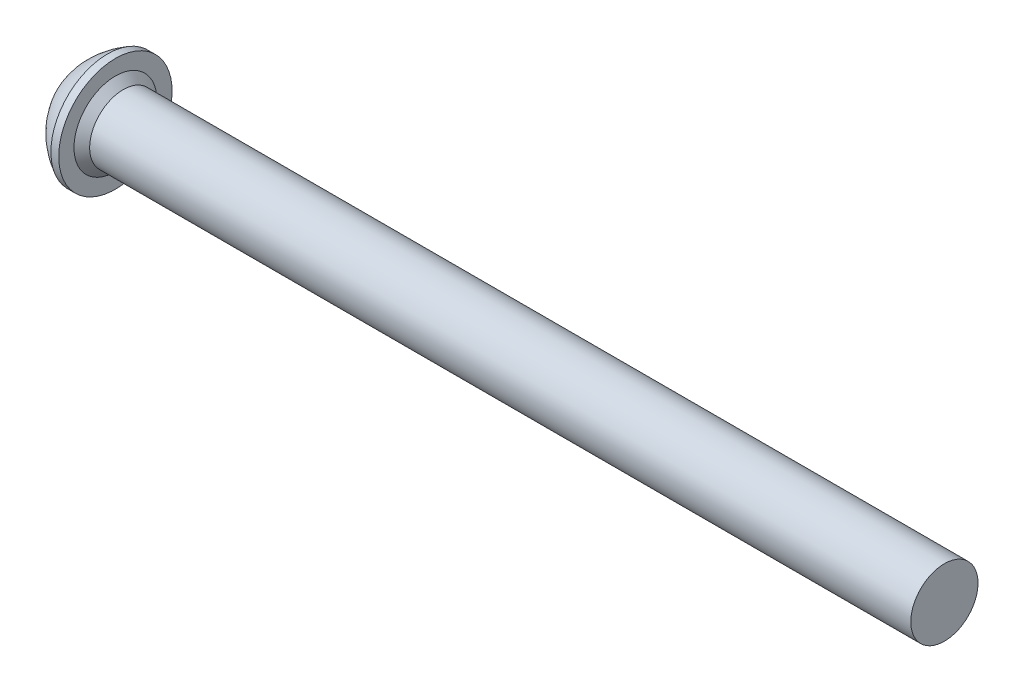
SolidWorks part; units mm, degrees
ref_plane "Front Plane" through (0, 0, 0) normal (0, 0, 1) x (1, 0, 0)
ref_plane "Top Plane" through (0, 0, 0) normal (0, 1, 0) x (1, 0, 0)
ref_plane "Right Plane" through (0, 0, 0) normal (1, 0, 0) x (0, 0, -1)
sketch "Sketch2" plane through (0, 0, 0) normal (0, 0, 1) x (1, 0, 0)
  line L0 (0, 0) -> (0, 1.43)
  line L2 (1.25, 2.53) -> (1.6, 2.53)
  line L3 (1.6, 2.53) -> (1.6, 1.85)
  line L4 (1.6, 1.85) -> (1.95, 1.5)
  line L5 (1.95, 1.5) -> (38.6, 1.5)
  line L6 (38.6, 1.5) -> (38.6, 0)
  line L7 (38.6, 0) -> (0, 0)
  arc A0 (1.25, 2.53) -> (0, 1.43) centre (2.8708, -0.5721) ccw
  point P10 (0.9983, 2.2125)
  point P11 (1.8687, 0.8411)
  point P12 (1.7013, 2.53)
  point P13 (1.95, 0.8645)
  point P14 (1.95, 0.835)
  point P15 (1.7135, 1.0417)
  point P16 (0.9606, 2.53)
  point P17 (1.6033, 1.8467)
  dimension "D4" = 3.5
  dimension "D1" = 1.43
  dimension "D2" = 1.95
  dimension "D3" = 0.35
  dimension "D5" = 2.53
  dimension "D6" = 135
  dimension "D7" = 1.5
  dimension "D8" = 0.35
  dimension "D9" = 37
revolve "Revolve1" add sketch "Sketch2" angle 360 about L7
sketch "Sketch3" plane through (0, 0, 0) normal (-1, 0, 0) x (0, 0, 1)
  line L0 (0, 2.3249) -> (0, -2.2676) construction
  line L2 (0, 1.1547) -> (-1, 0.5774)
  line L3 (-1, 0.5774) -> (-1, -0.5774)
  line L4 (-1, -0.5774) -> (0, -1.1547)
  line L5 (0, -1.1547) -> (1, -0.5774)
  line L6 (1, -0.5774) -> (1, 0.5774)
  line L7 (1, 0.5774) -> (0, 1.1547)
  circle A0 centre (0, 0) radius 1 construction
  dimension "D1" = 2
extrude "Cut-Extrude1" cut sketch "Sketch3" against normal blind 1
